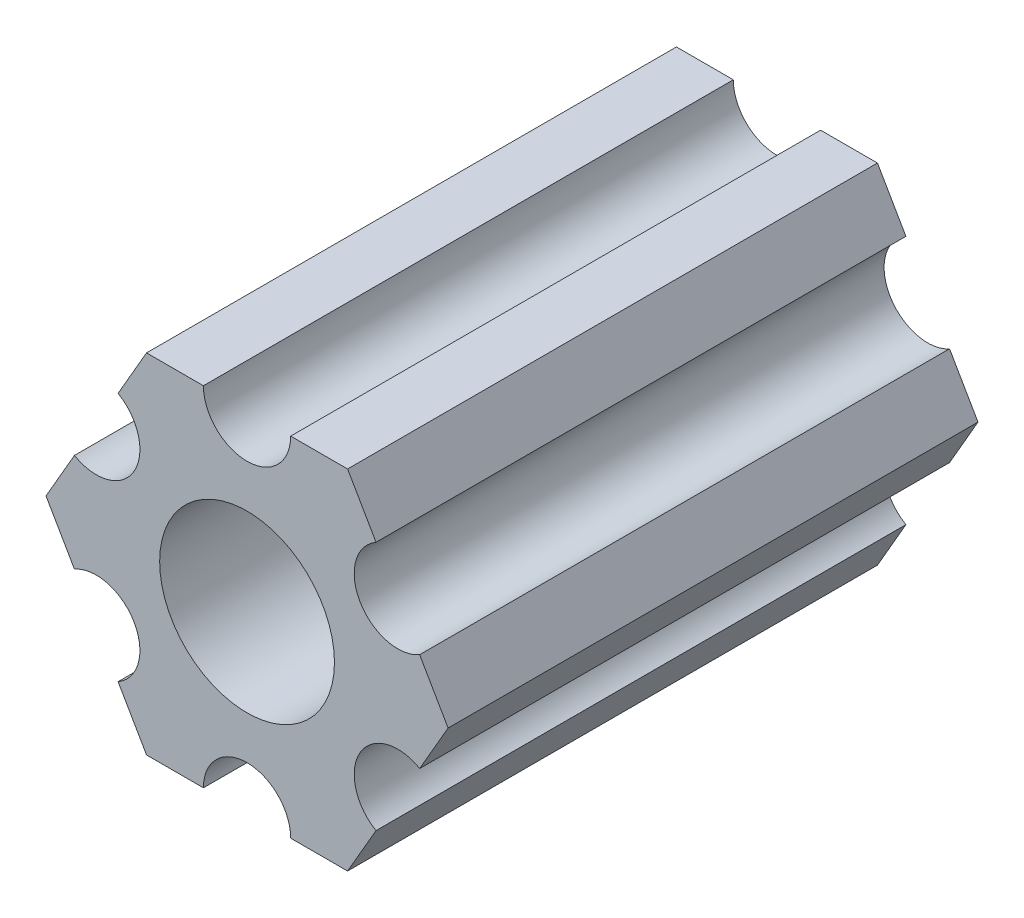
SolidWorks part; units mm, degrees
ref_plane "Front Plane" through (0, 0, 0) normal (0, 0, 1) x (1, 0, 0)
ref_plane "Top Plane" through (0, 0, 0) normal (0, 1, 0) x (1, 0, 0)
ref_plane "Right Plane" through (0, 0, 0) normal (1, 0, 0) x (0, 0, -1)
ref_plane "Plane1" through (0, 0, 0) normal (0, 0, -1) x (-1, 0, 0)
sketch "Sketch1" plane through (0, 0, 0) normal (0, 0, -1) x (-1, 0, 0)
  line L0 (-4.7036, -4.5531) -> (-3.6662, -6.35)
  line L1 (-3.6662, -6.35) -> (-1.5913, -6.35)
  line L2 (1.5913, -6.35) -> (3.6662, -6.35)
  line L3 (3.6662, -6.35) -> (4.7036, -4.5531)
  line L4 (6.2949, -1.7969) -> (7.3323, 0)
  line L5 (7.3323, 0) -> (6.2949, 1.7969)
  line L6 (4.7036, 4.5531) -> (3.6662, 6.35)
  line L7 (3.6662, 6.35) -> (1.5913, 6.35)
  line L8 (-1.5913, 6.35) -> (-3.6662, 6.35)
  line L9 (-3.6662, 6.35) -> (-4.7036, 4.5531)
  line L10 (-6.2949, 1.7969) -> (-7.3323, 0)
  line L11 (-7.3323, 0) -> (-6.2949, -1.7969)
  circle A0 centre (0, 0) radius 2.9337
  arc A1 (-6.2949, -1.7969) -> (-4.7036, -4.5531) centre (-5.4993, -3.175) cw
  arc A2 (-1.5913, -6.35) -> (1.5913, -6.35) centre (0, -6.35) cw
  arc A3 (4.7036, -4.5531) -> (6.2949, -1.7969) centre (5.4993, -3.175) cw
  arc A4 (6.2949, 1.7969) -> (4.7036, 4.5531) centre (5.4993, 3.175) cw
  arc A5 (1.5913, 6.35) -> (-1.5913, 6.35) centre (0, 6.35) cw
  arc A6 (-4.7036, 4.5531) -> (-6.2949, 1.7969) centre (-5.4993, 3.175) cw
extrude "Boss-Extrude1" add sketch "Sketch1" against normal blind 19.325
other "Move Face1" face at (2.9337, 0, 19.325) parameters "D1"=0.254
